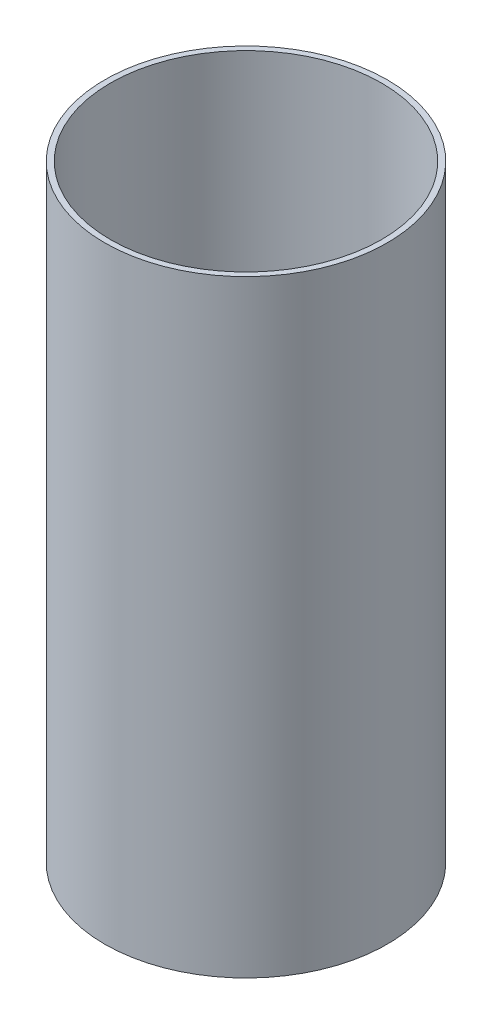
SolidWorks part; units mm, degrees
ref_plane "Front Plane" through (0, 0, 0) normal (0, 0, 1) x (1, 0, 0)
ref_plane "Top Plane" through (0, 0, 0) normal (0, 1, 0) x (1, 0, 0)
ref_plane "Right Plane" through (0, 0, 0) normal (1, 0, 0) x (0, 0, -1)
sketch "Sketch1" plane through (0, 0, 0) normal (0, 1, 0) x (1, 0, 0)
  circle A0 centre (0, 0) radius 38.1
  circle A1 centre (0, 0) radius 36.576
  dimension "D1" = 73.152
  dimension "D2" = 76.2
extrude "Boss-Extrude1" add sketch "Sketch1" along normal mid plane 163.83
ref_plane "Plane1" through (-38.1, 0, 0) normal (-1, 0, 0) x (0, 0, 1)
sketch "Sketch2" plane through (-38.1, 0, 0) normal (-1, 0, 0) x (0, 0, 1)
  circle A0 centre (0, 9.525) radius 6.985 construction
  circle A1 centre (0, 9.525) radius 6.985
extrude "Cut-Extrude1" cut sketch "Sketch2" against normal blind 6.35
equation "\"diameter\"= 3in"
equation "\"inner diameter\"= 2.88in"
equation "\"length\"= 6.45in"
